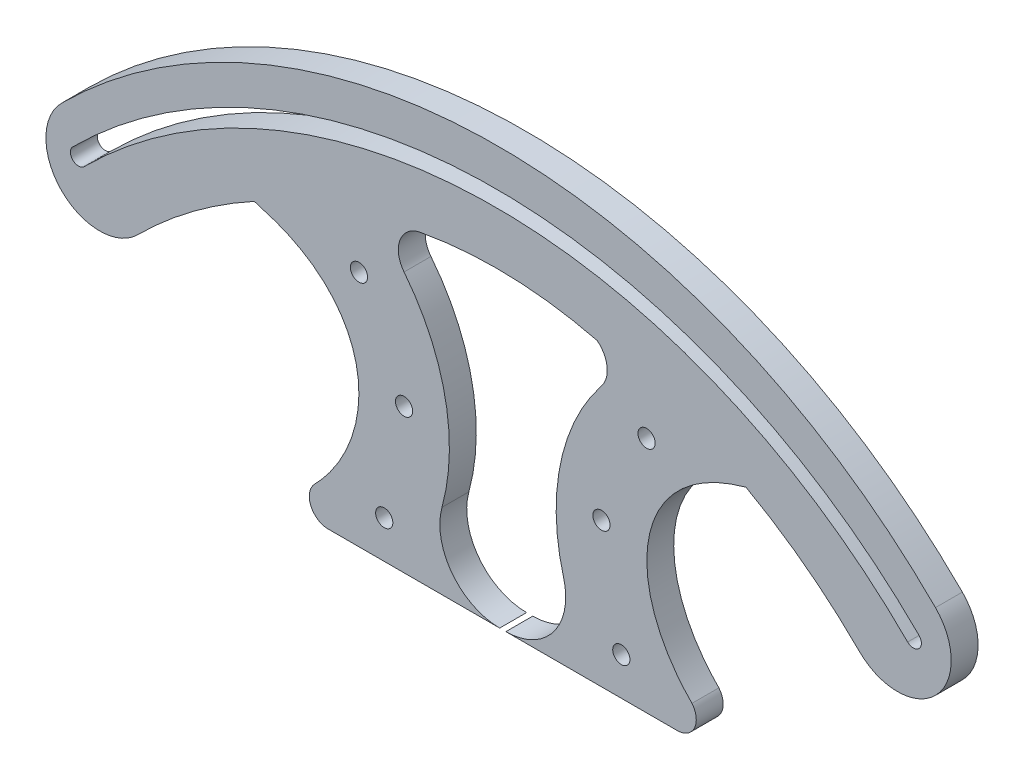
SolidWorks part; units mm, degrees
ref_plane "Front Plane" through (0, 0, 0) normal (0, 0, 1) x (1, 0, 0)
ref_plane "Top Plane" through (0, 0, 0) normal (0, 1, 0) x (1, 0, 0)
ref_plane "Right Plane" through (0, 0, 0) normal (1, 0, 0) x (0, 0, -1)
sketch "Sketch1" plane through (0, 0, 0) normal (0, 0, 1) x (1, 0, 0)
  line L0 (0, 75) -> (0, 29.4525) construction
  line L15 (-0.5732, 29.4525) -> (24.3745, 29.4525)
  line L16 (-24.3745, 29.4525) -> (-32.479, 29.4525)
  line L17 (-32.479, 29.4525) -> (24.3745, 29.4525)
  line L18 (24.3745, 29.4525) -> (32.479, 29.4525)
  line L19 (-75, 11.1914) -> (-75, 11.4006)
  line L20 (24.3745, 29.4525) -> (25.8496, 31.235) construction
  arc A0 (-75, 66.2145) -> (73.4291, 66.2145) centre (-0.7855, -8) cw construction
  arc A1 (80.5002, 73.2856) -> (-82.0711, 73.2856) centre (-0.7855, -8) ccw
  arc A2 (66.358, 59.1435) -> (45.2421, 75.054) centre (-0.7855, -8) ccw
  arc A3 (66.358, 59.1435) -> (80.5002, 73.2856) centre (73.4291, 66.2145) ccw
  arc A4 (-82.0711, 73.2856) -> (-67.9289, 59.1435) centre (-75, 66.2145) ccw
  arc A5 (-11.3131, 43.5336) -> (-18.3641, 77.9294) centre (-48.71, 53.788) ccw
  arc A6 (11.3131, 43.5336) -> (18.3641, 77.9294) centre (48.71, 53.788) cw
  arc A7 (-15.2684, 85.8442) -> (-18.3641, 77.9294) centre (-14.519, 80.9883) ccw
  arc A8 (-67.9289, 59.1435) -> (-46.2299, 75.3744) centre (-0.7855, -8) cw
  arc A9 (17.5613, 84.8465) -> (18.3641, 77.9294) centre (14.519, 80.9883) cw
  arc A10 (-0.5732, 29.4525) -> (-11.3131, 43.5336) centre (-0.5732, 40.5887) cw
  arc A11 (0.5732, 29.4525) -> (11.3131, 43.5336) centre (0.5732, 40.5887) ccw
  circle A12 centre (-18.3641, 56.2921) radius 1.6
  circle A13 centre (-26.7535, 73.6912) radius 1.6
  circle A14 centre (-22.0529, 36.4833) radius 1.6
  circle A15 centre (22.0529, 36.4833) radius 1.6
  circle A16 centre (26.7535, 73.6912) radius 1.6
  circle A17 centre (18.3641, 56.2921) radius 1.6
  arc A18 (-32.479, 29.4525) -> (-35.002, 35.4282) centre (-32.479, 32.973) cw
  arc A19 (32.479, 29.4525) -> (35.002, 35.4282) centre (32.479, 32.973) ccw
  arc A20 (17.5613, 84.8465) -> (-15.2684, 85.8442) centre (-1.1547, 9.6252) ccw
  arc A21 (-78.9419, 66.2145) -> (76.3841, 66.2145) centre (-1.2789, -11.4485) cw construction
  arc A22 (77.4448, 67.2752) -> (-80.0026, 67.2752) centre (-1.2789, -11.4485) ccw
  arc A23 (75.3234, 65.1539) -> (-77.8813, 65.1539) centre (-1.2789, -11.4485) ccw
  arc A24 (75.3234, 65.1539) -> (77.4448, 67.2752) centre (76.3841, 66.2145) ccw
  arc A25 (-80.0026, 67.2752) -> (-77.8813, 65.1539) centre (-78.9419, 66.2145) ccw
  spline S0 degree 3 poles (-45.0557, 75) (-29.9457, 70.8925) (-22.5995, 54.7742) (-31.1258, 39.4113) (-35.002, 35.4282) knots 0.154809 0.154809 0.154809 0.154809 0.468621 0.606167 0.606167 0.606167 0.606167
  spline S1 degree 3 poles (45.2421, 75.054) (30.1321, 70.9465) (22.5401, 54.6807) (31.1995, 39.2379) (35.1967, 35.2108) knots 0.154809 0.154809 0.154809 0.154809 0.468621 0.608629 0.608629 0.608629 0.608629
  spline S2 degree 1 poles (-45.0557, 75) (-46.2299, 75.3744) knots 0 0 1 1
  spline S3 degree 2 poles (-75, 11.4006) (-75.001, 11.2967) (-75, 11.1914) knots 0.998195 0.998195 0.998195 1 1 1
  point P0 (0, 0)
  point P26 (-1.2789, 98.3836)
  point P31 (-0.7855, 96.9552)
  dimension "D1" = 3.5205
  dimension "D3" = 4.9134
  dimension "D4" = 11.1362
  dimension "D5" = 3.2
extrude "Boss-Extrude1" add sketch "Sketch1" along normal blind 5 contours S2 S0 A18 L16 L17 A10 A5 A7 A20 A9 A6 A11 L18 A19 S1 A2 A3 A1 A4 A8 A25 A22 A24 A23 A16 A12 A13 A14 A15 A17
